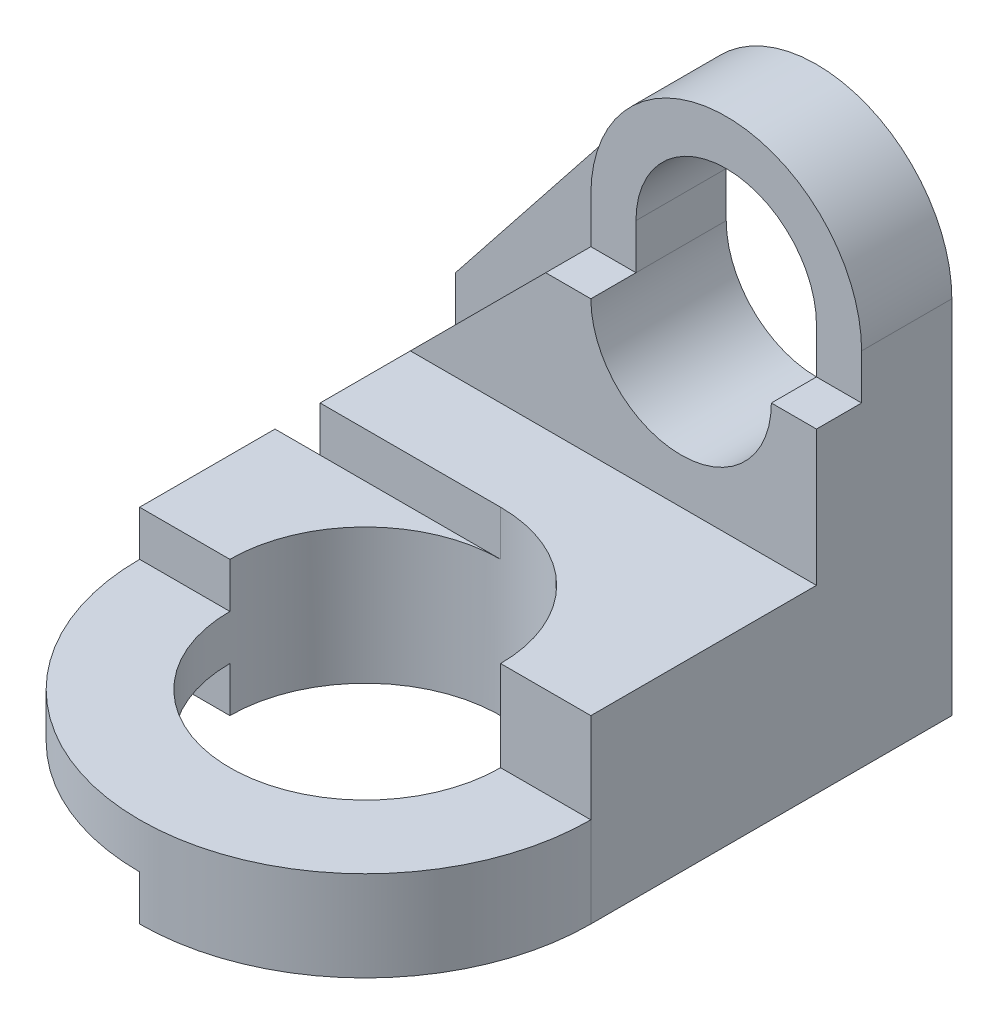
SolidWorks part; units mm, degrees
ref_plane "Front Plane" through (0, 0, 0) normal (0, 0, 1) x (1, 0, 0)
ref_plane "Top Plane" through (0, 0, 0) normal (0, 1, 0) x (1, 0, 0)
ref_plane "Right Plane" through (0, 0, 0) normal (1, 0, 0) x (0, 0, -1)
sketch "Sketch2" plane through (0, 0, 0) normal (0, 0, 1) x (1, 0, 0)
  line L0 (0, 0) -> (0, 4)
  line L2 (7, 8) -> (7, 7) construction
  line L3 (9, 8) -> (9, 7)
  line L4 (5, 8) -> (5, 7)
  line L5 (7, 8) -> (7, 7) construction
  line L8 (10, 8) -> (10, 0)
  line L9 (10, 0) -> (0, 0)
  line L10 (0, 4) -> (4.6492, 9.8638)
  arc A0 (9, 8) -> (5, 8) centre (7, 8) ccw
  arc A1 (5, 7) -> (9, 7) centre (7, 7) ccw
  arc A2 (10, 8) -> (4.6492, 9.8638) centre (7, 8) ccw
  point P6 (7, 7.5)
  point P13 (7, 7.5)
  dimension "D5" = 2
  dimension "D6" = 10
  dimension "D8" = 3
  dimension "D1" = 4
  dimension "D2" = 1
  dimension "D4" = 8
  dimension "D7" = 1
extrude "Boss-Extrude1" add sketch "Sketch2" along normal blind 1
sketch "Sketch3" plane through (0, 0, 1) normal (0, 0, 1) x (1, 0, 0)
  line L0 (1, 0) -> (1, 4)
  line L1 (10, 0) -> (0, 0) construction
  line L2 (1, 4) -> (4, 7)
  line L3 (0, 0) -> (0, 4) construction
  line L4 (7, 7) -> (7, 8) construction
  line L5 (5, 7) -> (5, 8)
  line L6 (9, 7) -> (9, 8)
  line L7 (7, 7) -> (7, 8) construction
  line L8 (4, 7) -> (4, 8)
  line L9 (10, 7) -> (10, 8)
  line L10 (10, 7) -> (10, 0)
  line L11 (10, 0) -> (1, 0)
  arc A0 (5, 7) -> (9, 7) centre (7, 7) ccw
  arc A1 (9, 8) -> (5, 8) centre (7, 8) ccw
  arc A2 (10, 8) -> (4.6492, 9.8638) centre (7, 8) ccw construction
  arc A4 (4, 7) -> (10, 7) centre (7, 7) ccw
  arc A5 (10, 8) -> (4, 8) centre (7, 8) ccw
  point P10 (7, 7.5)
  point P17 (7, 7.5)
  arc M1 (9, 7) -> (5, 7) centre (7, 7) cw
  line M2 (5, 7) -> (5, 8)
  arc M3 (5, 8) -> (9, 8) centre (7, 8) cw
  line M4 (9, 8) -> (9, 7)
  line M5 (10, 0) -> (10, 8)
  arc M6 (10, 8) -> (4.6492, 9.8638) centre (7, 8) ccw
  line M9 (0, 0) -> (10, 0)
  dimension "D4" = 2
  dimension "D5" = 3
  dimension "D6" = 3
  dimension "D1" = 1
  dimension "D2" = 4
  dimension "D3" = 3
  dimension "D7" = 1
extrude "Boss-Extrude3" add sketch "Sketch3" along normal blind 2 contours A4 L8 L2 L0 M9 M5 | A5 L8 A4 M6 M5 M4 M1 M2 M3
sketch "Sketch5" plane through (0, 0, 3) normal (0, 0, 1) x (1, 0, 0)
  line L1 (4, 7) -> (10.3234, 7)
  line L2 (4, 7) -> (4, 11.4057)
  line L3 (4, 11.4057) -> (10.3234, 11.4057)
  line L4 (10.3234, 7) -> (10.3234, 11.4057)
extrude "Cut-Extrude2" cut sketch "Sketch5" against normal blind 1
sketch "Sketch6" plane through (0, 0, 3) normal (0, 0, 1) x (1, 0, 0)
  line L1 (1, 4) -> (10, 4)
  line L2 (1, 4) -> (1, 0)
  line L3 (1, 0) -> (10, 0)
  line L4 (10, 4) -> (10, 0)
extrude "Boss-Extrude4" add sketch "Sketch6" along normal blind 2
sketch "Sketch7" plane through (0, 0, 5) normal (0, 0, 1) x (1, 0, 0)
  line L1 (0, 3) -> (10, 3)
  line L2 (0, 3) -> (0, 0)
  line L3 (0, 0) -> (10, 0)
  line L4 (10, 3) -> (10, 0)
  line L5 (1, 4) -> (1, 0) construction
  line L6 (10, 4) -> (1, 4) construction
  dimension "D1" = 3
  dimension "D2" = 10
  dimension "D3" = 1
  dimension "D4" = 1
extrude "Boss-Extrude5" add sketch "Sketch7" along normal blind 8
sketch "Sketch8" plane through (0, 4, 0) normal (0, 1, 0) x (1, 0, 0)
  line L0 (10, -13) -> (10, -5) construction
  line L5 (10, -13) -> (0, -13) construction
  line L6 (10, -8) -> (10, -16.3168)
  line L7 (10, -16.3168) -> (0, -16.3168)
  line L8 (0, -16.3168) -> (0, -8)
  circle A0 centre (5, -8) radius 5
  circle A1 centre (5, -8) radius 3
  point P0 (5, -8)
  dimension "D3" = 6
  dimension "D1" = 5
  dimension "D2" = 5
extrude "Cut-Extrude3" cut sketch "Sketch8" against normal blind 8 contours A0 L8 L7 L6 | A1
sketch "Sketch9" plane through (0, 0, 0) normal (0, -1, 0) x (1, 0, 0)
  line L0 (5, 11) -> (5, 13)
  line L1 (2, 8) -> (0, 8)
  arc A0 (5, 13) -> (0, 8) centre (5, 8) ccw
  arc A1 (10, 8) -> (0, 8) centre (5, 8) ccw construction
  arc A2 (5, 11) -> (2, 8) centre (5, 8) ccw
  circle A3 centre (5, 8) radius 3 construction
extrude "Cut-Extrude4" cut sketch "Sketch9" against normal blind 1
sketch "Sketch10" plane through (0, 3, 0) normal (0, 1, 0) x (1, 0, 0)
  line L0 (0, -8) -> (2, -8)
  line L1 (8, -8) -> (10, -8)
  arc A0 (0, -8) -> (10, -8) centre (5, -8) ccw
  arc A1 (8, -8) -> (2, -8) centre (5, -8) cw
  circle A2 centre (5, -8) radius 3 construction
extrude "Cut-Extrude5" cut sketch "Sketch10" against normal blind 1
sketch "Sketch11" plane through (0, 3, 0) normal (0, 1, 0) x (1, 0, 0)
  line L0 (8, -8) -> (10, -8)
  line L1 (10, -8) -> (10, -5)
  line L2 (10, -5) -> (5, -5)
  arc A0 (5, -5) -> (8, -8) centre (5, -8) cw
extrude "Boss-Extrude6" add sketch "Sketch11" along normal blind 1
